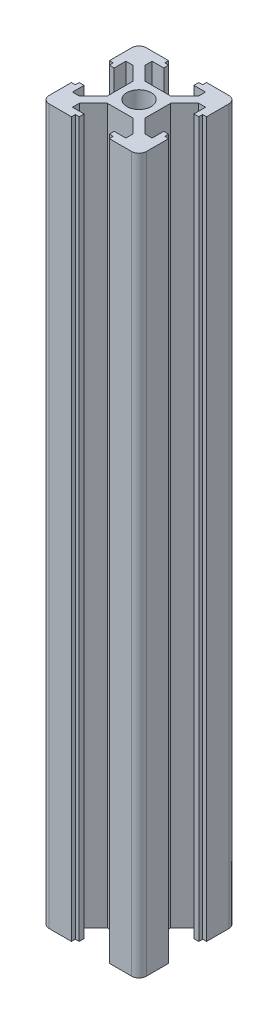
SolidWorks part; units mm, degrees
material "6063-O"
ref_plane "Front Plane" through (0, 0, 0) normal (0, 0, 1) x (1, 0, 0)
ref_plane "Top Plane" through (0, 0, 0) normal (0, 1, 0) x (1, 0, 0)
ref_plane "Right Plane" through (0, 0, 0) normal (1, 0, 0) x (0, 0, -1)
sketch "Sketch1" plane through (0, 0, 0) normal (0, 1, 0) x (1, 0, 0)
  line L0 (0, 14.5399) -> (0, 10) construction
  line L1 (-16.8658, 0) -> (2.5, 0) construction
  line L2 (13.2784, 3.9) -> (3.9, 3.9) construction
  line L3 (0, 0) -> (2.5, 0)
  line L4 (0, 0) -> (0, 2.5)
  line L5 (3.9, 10) -> (8.5, 10)
  line L6 (9.2, 0) -> (16.4291, 0) construction
  line L7 (-2.63, 3.9) -> (2.63, 3.9)
  line L9 (2.5491, 3.9) -> (2.63, 3.9)
  line L10 (3.9, 0) -> (3.9, 2.63)
  line L11 (13.2784, 3.1) -> (2.5491, 3.1) construction
  line L12 (8.2, 7.5573) -> (8.2, -3.0868) construction
  line L13 (9.2, 7.2593) -> (9.2, -8.1534) construction
  line L14 (10, 3.9) -> (9.2, 3.9)
  line L15 (9.2, 3.9) -> (9.2, 3.1)
  line L16 (9.2, 3.1) -> (8.2, 3.1)
  line L17 (8.2, 3.1) -> (8.2, 5.5)
  line L18 (8.2, 5.5) -> (6.77, 5.5)
  line L19 (6.77, 5.5) -> (3.9, 2.63)
  line L20 (5.0973, 5.5) -> (13.0082, 5.5) construction
  line L21 (3.1, 11.2046) -> (3.1, 2.6994) construction
  line L22 (3.9, 10.7498) -> (3.9, 3.9) construction
  line L23 (5.5, 11.523) -> (5.5, 1.4941) construction
  line L24 (-2.2597, 8.2) -> (6.1545, 8.2) construction
  line L25 (-2.9419, 9.2) -> (5.7225, 9.2) construction
  line L26 (3.9, 10) -> (3.9, 9.2)
  line L27 (3.9, 9.2) -> (3.1, 9.2)
  line L28 (3.1, 9.2) -> (3.1, 8.2)
  line L29 (3.1, 8.2) -> (5.5, 8.2)
  line L30 (5.5, 8.2) -> (5.5, 6.77)
  line L31 (5.5, 6.77) -> (2.63, 3.9)
  line L32 (0, 2.5) -> (0, -14.4122) construction
  line L33 (10, 3.9) -> (10, 8.5)
  line L34 (9.2, 0) -> (10, 0)
  line L35 (2.63, 3.9) -> (2.5491, 3.9) construction
  line L36 (3.9, 2.63) -> (3.9, 2.0627) construction
  line L37 (10, -3.9) -> (10, -8.5)
  line L38 (3.9, -10) -> (8.5, -10)
  line L39 (3.9, -10) -> (3.9, -9.2)
  line L40 (3.9, -9.2) -> (3.1, -9.2)
  line L41 (3.1, -9.2) -> (3.1, -8.2)
  line L42 (3.1, -8.2) -> (5.5, -8.2)
  line L43 (5.5, -8.2) -> (5.5, -6.77)
  line L44 (5.5, -6.77) -> (2.63, -3.9)
  line L45 (0, -3.9) -> (2.63, -3.9)
  line L46 (3.9, 0) -> (3.9, -2.63)
  line L47 (6.77, -5.5) -> (3.9, -2.63)
  line L48 (8.2, -5.5) -> (6.77, -5.5)
  line L49 (8.2, -3.1) -> (8.2, -5.5)
  line L50 (9.2, -3.1) -> (8.2, -3.1)
  line L51 (9.2, -3.9) -> (9.2, -3.1)
  line L52 (10, -3.9) -> (9.2, -3.9)
  line L53 (-3.9, -10) -> (-8.5, -10)
  line L54 (-10, -3.9) -> (-10, -8.5)
  line L55 (-10, -3.9) -> (-9.2, -3.9)
  line L56 (-9.2, -3.9) -> (-9.2, -3.1)
  line L57 (-9.2, -3.1) -> (-8.2, -3.1)
  line L58 (-8.2, -3.1) -> (-8.2, -5.5)
  line L59 (-8.2, -5.5) -> (-6.77, -5.5)
  line L60 (-6.77, -5.5) -> (-3.9, -2.63)
  line L61 (-3.9, 0) -> (-3.9, -2.63)
  line L62 (0, -3.9) -> (-2.63, -3.9)
  line L63 (-5.5, -6.77) -> (-2.63, -3.9)
  line L64 (-5.5, -8.2) -> (-5.5, -6.77)
  line L65 (-3.1, -8.2) -> (-5.5, -8.2)
  line L66 (-3.1, -9.2) -> (-3.1, -8.2)
  line L67 (-3.9, -9.2) -> (-3.1, -9.2)
  line L68 (-3.9, -10) -> (-3.9, -9.2)
  line L69 (-10, 3.9) -> (-10, 8.5)
  line L70 (-3.9, 10) -> (-8.5, 10)
  line L71 (-3.9, 10) -> (-3.9, 9.2)
  line L72 (-3.9, 9.2) -> (-3.1, 9.2)
  line L73 (-3.1, 9.2) -> (-3.1, 8.2)
  line L74 (-3.1, 8.2) -> (-5.5, 8.2)
  line L75 (-5.5, 8.2) -> (-5.5, 6.77)
  line L76 (-5.5, 6.77) -> (-2.63, 3.9)
  line L78 (-3.9, 0) -> (-3.9, 2.63)
  line L79 (-6.77, 5.5) -> (-3.9, 2.63)
  line L80 (-8.2, 5.5) -> (-6.77, 5.5)
  line L81 (-8.2, 3.1) -> (-8.2, 5.5)
  line L82 (-9.2, 3.1) -> (-8.2, 3.1)
  line L83 (-9.2, 3.9) -> (-9.2, 3.1)
  line L84 (-10, 3.9) -> (-9.2, 3.9)
  line L85 (0, 3.9) -> (-2.63, 3.9) [skipped]
  circle A0 centre (0, 0) radius 2.5
  arc A1 (8.5, 10) -> (10, 8.5) centre (8.5, 8.5) cw
  arc A2 (10, -8.5) -> (8.5, -10) centre (8.5, -8.5) cw
  arc A4 (-8.5, -10) -> (-10, -8.5) centre (-8.5, -8.5) cw
  arc A6 (-10, 8.5) -> (-8.5, 10) centre (-8.5, 8.5) cw
  point P12 (10, 10)
  point P126 (0, 0)
  dimension "D3" = 5
  dimension "D4" = 1.5
  dimension "D1" = 10
  dimension "D2" = 10
  dimension "D6" = 3.9
  dimension "D7" = 3.9
  dimension "D8" = 3.1
  dimension "D9" = 4
  dimension "D11" = 5.5
  dimension "D12" = 1.8
  dimension "D13" = 0.8
  dimension "D14" = 3.9
  dimension "D15" = 3.1
  dimension "D16" = 5.5
  dimension "D17" = 1.27
  dimension "D18" = 1.27
  dimension "D19" = 1.27
  dimension "D20" = 1.27
extrude "Boss-Extrude1" add sketch "Sketch1" along normal blind 147 contours A6 L69 L84 L83 L82 L81 L80 L79 L78 L61 L60 L59 L58 L57 L56 L55 L54 A4 L53 L68 L67 L66 L65 L64 L63 L62 L45 L44 L43 L42 L41 L40 L39 L38 A2 L37 L52 L51 L50 L49 L48 L47 L46 L10 L19 L18 L17 L16 L15 L14 L33
